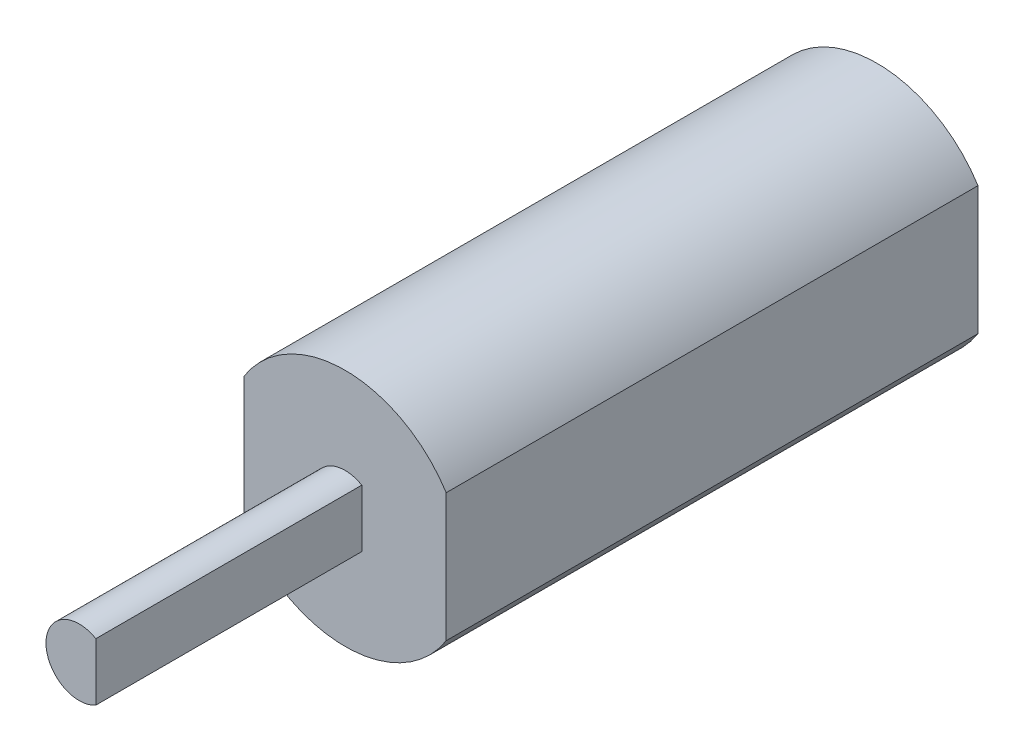
SolidWorks part; units mm, degrees
material "1060 Alloy"
ref_plane "Front Plane" through (0, 0, 0) normal (0, 0, 1) x (1, 0, 0)
ref_plane "Top Plane" through (0, 0, 0) normal (0, 1, 0) x (1, 0, 0)
ref_plane "Right Plane" through (0, 0, 0) normal (1, 0, 0) x (0, 0, -1)
sketch "Sketch1" plane through (0, 0, 0) normal (0, 0, 1) x (1, 0, 0)
  line L2 (-4.826, 0.0167) -> (-4.826, -3.0445)
  line L3 (-4.826, 0.0167) -> (-4.826, 3.0779)
  line L4 (4.826, 0.0167) -> (4.826, -3.0445)
  line L5 (4.826, 0.0167) -> (4.826, 3.0779)
  arc A0 (4.826, 3.0779) -> (-4.826, 3.0779) centre (0, 0.0167) ccw
  arc A1 (-4.826, -3.0445) -> (4.826, -3.0445) centre (0, 0.0167) ccw
  dimension "D1" = 11.43
  dimension "D2" = 4.826
  dimension "D3" = 4.826
extrude "Boss-Extrude1" add sketch "Sketch1" along normal blind 25.4
sketch "Sketch2" plane through (0, 0, 25.4) normal (0, 0, 1) x (1, 0, 0)
  line L1 (0.7938, 0) -> (0.7938, 1.3748)
  line L2 (0.7938, 0) -> (0.7938, -1.3748)
  arc A0 (0.7938, 1.3748) -> (0.7938, -1.3748) centre (0, 0) ccw
  dimension "D1" = 3.175
extrude "Boss-Extrude2" add sketch "Sketch2" along normal blind 12.7
